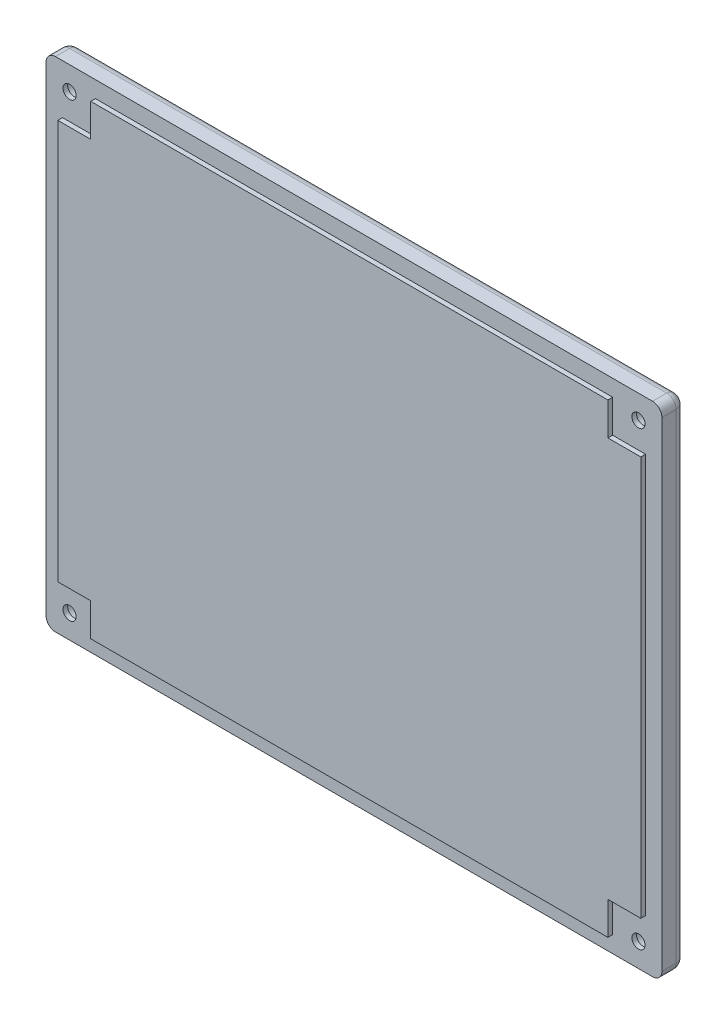
SolidWorks part; units mm, degrees
ref_plane "Front Plane" through (0, 0, 0) normal (0, 0, 1) x (1, 0, 0)
ref_plane "Top Plane" through (0, 0, 0) normal (0, 1, 0) x (1, 0, 0)
ref_plane "Right Plane" through (0, 0, 0) normal (1, 0, 0) x (0, 0, -1)
sketch "Sketch1" plane through (0, 0, 0) normal (0, 0, 1) x (1, 0, 0)
  line L1 (0, 0) -> (131, 0)
  line L2 (0, 0) -> (0, 106)
  line L3 (0, 106) -> (131, 106)
  line L4 (131, 0) -> (131, 106)
  dimension "D1" = 131
  dimension "D2" = 106
extrude "Boss-Extrude1" add sketch "Sketch1" along normal blind 5
sketch "Sketch6" plane through (0, 0, 0) normal (0, 0, -1) x (-1, 0, 0)
  line L0 (0, 0) -> (-131, 0) construction
  line L1 (0, 106) -> (0, 0) construction
  circle A0 centre (-5, 5) radius 2
  dimension "D1" = 5
  dimension "D2" = 5
extrude "Cut-Extrude1" cut sketch "Sketch6" against normal blind 4
sketch "Sketch7" plane through (0, 0, 4) normal (0, 0, -1) x (-1, 0, 0)
  line L0 (0, 0) -> (-131, 0) construction
  line L1 (0, 106) -> (0, 0) construction
  circle A0 centre (-5, 5) radius 1.4
  dimension "D1" = 5
  dimension "D2" = 5
extrude "Cut-Extrude2" cut sketch "Sketch7" against normal blind 2.8
ref_plane "Plane1" through (0, 53, 0) normal (0, -1, 0) x (-1, 0, 0)
ref_plane "Plane2" through (65.5, 0, 0) normal (-1, 0, 0) x (0, 0, 1)
mirror "Mirror1" about plane through (65.5, 0, 0) normal (-1, 0, 0) of "Cut-Extrude2", "Cut-Extrude1"
mirror "Mirror2" about plane through (0, 53, 0) normal (0, -1, 0) of "Mirror1", "Cut-Extrude1", "Cut-Extrude2"
sketch "Sketch8" plane through (0, 0, 5) normal (0, 0, 1) x (1, 0, 0)
  line L0 (131, 106) -> (0, 106) construction
  line L1 (120.5, 102.5) -> (10.5, 102.5)
  line L2 (120.5, 102.5) -> (120.5, 3.5)
  line L3 (120.5, 3.5) -> (10.5, 3.5)
  line L4 (10.5, 102.5) -> (10.5, 3.5)
  line L5 (131, 0) -> (131, 106) construction
  line L6 (0, 0) -> (131, 0) construction
  line L7 (0, 106) -> (0, 0) construction
  dimension "D1" = 3.5
  dimension "D2" = 10.5
  dimension "D3" = 3.5
  dimension "D4" = 10.5
sketch "Sketch10" plane through (0, 0, 0) normal (0, 0, -1) x (-1, 0, 0)
  line L0 (0, 0) -> (-131, 0) construction
  line L1 (-101, 20) -> (-61, 20)
  line L2 (-101, 20) -> (-101, 86)
  line L3 (-101, 86) -> (-61, 86)
  line L4 (-61, 20) -> (-61, 86)
  line L5 (-131, 106) -> (0, 106) construction
  line L6 (-131, 0) -> (-131, 106) construction
  dimension "D1" = 20
  dimension "D2" = 20
  dimension "D3" = 30
  dimension "D4" = 40
extrude "Cut-Extrude5" cut sketch "Sketch10" against normal blind 1
fillet "Fillet1" radius 2 8 edges at (131, 106, 2.5) (131, 0, 2.5) (0, 0, 2.5) (0, 106, 2.5) (0, 53, 0) (131, 53, 0) (65.5, 106, 0) (65.5, 0, 0)
extrude "Boss-Extrude2" add sketch "Sketch8" along normal blind 1
sketch "Sketch11" plane through (0, 0, 5) normal (0, 0, 1) x (1, 0, 0)
  line L0 (10.5, 102.5) -> (10.5, 3.5) construction
  line L1 (3.5, 10.5) -> (10.5, 10.5)
  line L2 (3.5, 10.5) -> (3.5, 95.5)
  line L3 (3.5, 95.5) -> (10.5, 95.5)
  line L4 (10.5, 10.5) -> (10.5, 95.5)
  line L5 (2, 0) -> (129, 0) construction
  line L6 (129, 106) -> (2, 106) construction
  line L7 (0, 104) -> (0, 2) construction
  dimension "D1" = 10.5
  dimension "D2" = 10.5
  dimension "D3" = 3.5
extrude "Boss-Extrude3" add sketch "Sketch11" along normal blind 1
mirror "Mirror3" about plane through (65.5, 0, 0) normal (-1, 0, 0) of "Boss-Extrude3"
